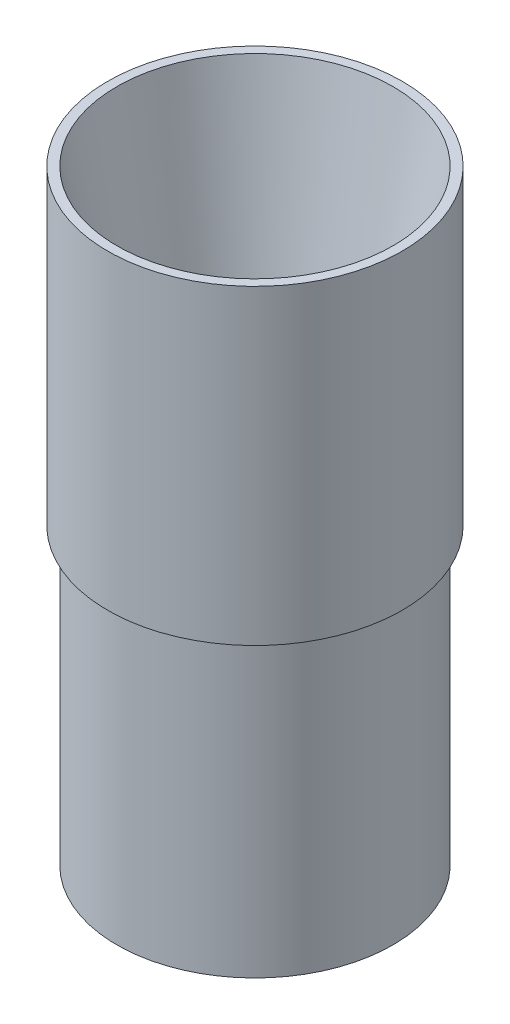
SolidWorks part; units mm, degrees
material "6061-T6 (SS)"
ref_plane "Front Plane" through (0, 0, 0) normal (0, 0, 1) x (1, 0, 0)
ref_plane "Top Plane" through (0, 0, 0) normal (0, 1, 0) x (1, 0, 0)
ref_plane "Right Plane" through (0, 0, 0) normal (1, 0, 0) x (0, 0, -1)
sketch "Sketch1" plane through (0, 0, 0) normal (0, 0, 1) x (1, 0, 0)
  line L0 (0, 0) -> (24.2189, 0) construction
  line L1 (24.2189, 0) -> (47.625, 132.7426)
  line L2 (47.625, 132.7426) -> (50.8, 132.7426)
  line L3 (50.8, 132.7426) -> (50.8, 25.4)
  line L4 (50.8, 25.4) -> (47.625, 25.4)
  line L5 (47.625, 25.4) -> (47.625, -76.2)
  line L6 (47.625, -76.2) -> (41.275, -76.2)
  line L7 (41.275, -76.2) -> (41.275, 0)
  line L8 (41.275, 0) -> (24.2189, 0)
  line L9 (0, 0) -> (0, 28.4315) construction
  dimension "D1" = 80
  dimension "D2" = 24.2189
  dimension "D3" = 50.8
  dimension "D4" = 3.175
  dimension "D5" = 6.35
  dimension "D6" = 101.6
  dimension "D7" = 76.2
revolve "Revolve1" add sketch "Sketch1" angle 360 about L9
